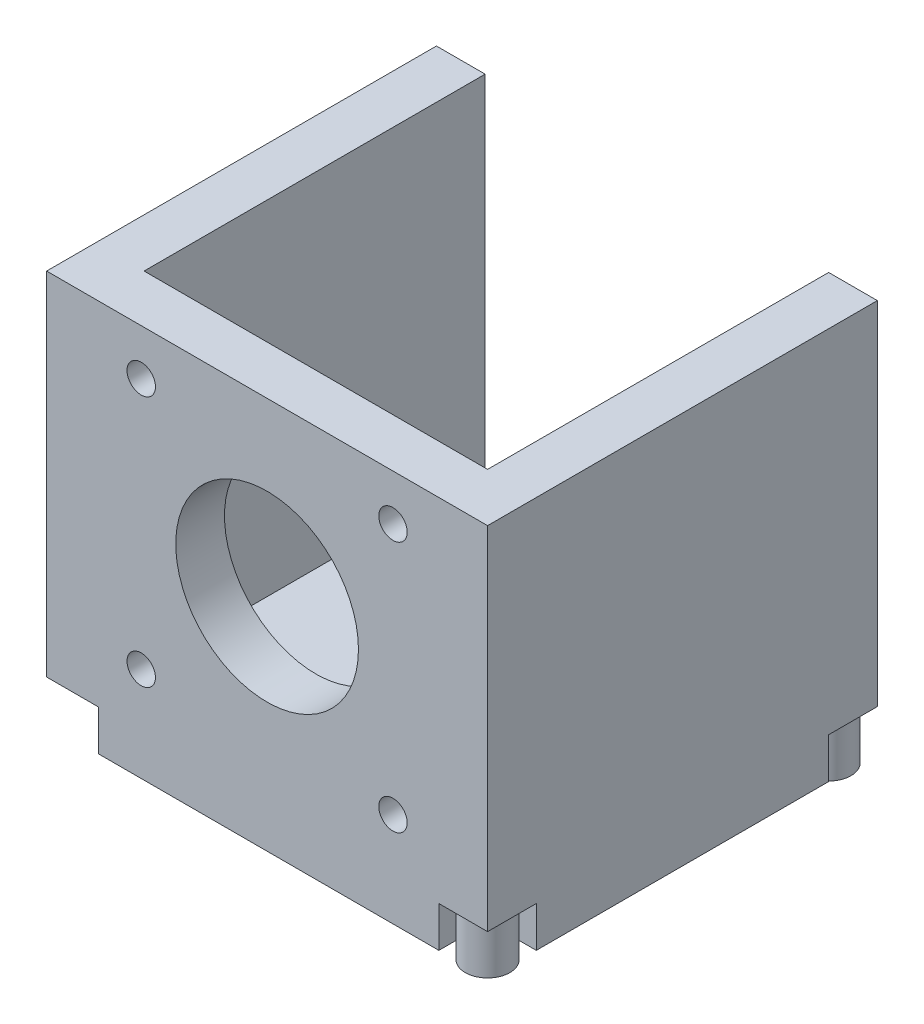
SolidWorks part; units mm, degrees
ref_plane "Спереди" through (0, 0, 0) normal (0, 0, 1) x (1, 0, 0)
ref_plane "Сверху" through (0, 0, 0) normal (0, 1, 0) x (1, 0, 0)
ref_plane "Справа" through (0, 0, 0) normal (1, 0, 0) x (0, 0, -1)
sketch "Эскиз1" plane through (0, 0, 0) normal (0, 0, 1) x (1, 0, 0)
  line L0 (21.15, 42.3) -> (21.15, 0) construction
  line L1 (42.3, 42.3) -> (0, 42.3)
  line L2 (42.3, 42.3) -> (42.3, 0)
  line L3 (42.3, 0) -> (0, 0)
  line L4 (0, 42.3) -> (0, 0)
  line L5 (0, 21.15) -> (42.3, 21.15) construction
  circle A0 centre (36.65, 36.65) radius 1.75
  circle A1 centre (5.65, 36.65) radius 1.75
  circle A2 centre (5.65, 5.65) radius 1.75
  circle A3 centre (36.65, 5.65) radius 1.75
  circle A4 centre (21.15, 21.15) radius 11.25
  dimension "D3" = 3.5
  dimension "D8" = 22.5
  dimension "D1" = 42.3
  dimension "D2" = 42.3
  dimension "D4" = 15.5
  dimension "D5" = 15.5
  dimension "D6" = 2
  dimension "D7" = 2
extrude "Бобышка-Вытянуть1" add sketch "Эскиз1" along normal blind 6
sketch "Эскиз2" plane through (0, 0, 0) normal (-1, 0, 0) x (0, 0, 1)
  line L0 (6, 42.3) -> (-42, 42.3)
  line L1 (-42, 42.3) -> (-42, 0)
  line L2 (-42, 0) -> (6, 0)
  line L3 (6, 0) -> (6, 42.3)
  dimension "D1" = 48
extrude "Бобышка-Вытянуть2" add sketch "Эскиз2" along normal blind 6
sketch "Эскиз3" plane through (42.3, 0, 0) normal (1, 0, 0) x (0, 0, -1)
  line L0 (-6, 42.3) -> (42, 42.3)
  line L1 (42, 42.3) -> (42, 0)
  line L2 (42, 0) -> (-6, 0)
  line L3 (-6, 0) -> (-6, 42.3)
  dimension "D1" = 48
extrude "Бобышка-Вытянуть3" add sketch "Эскиз3" along normal blind 6
sketch "Эскиз4" plane through (0, 0, 0) normal (0, -1, 0) x (1, 0, 0)
  line L0 (-6, -42) -> (48.3, -42)
  line L1 (48.3, -42) -> (48.3, 6)
  line L2 (48.3, 6) -> (-6, 6)
  line L3 (-6, 6) -> (-6, -42)
extrude "Бобышка-Вытянуть4" add sketch "Эскиз4" along normal blind 6
sketch "Эскиз5" plane through (0, -6, 0) normal (0, -1, 0) x (1, 0, 0)
  line L0 (-6, -42) -> (0, -42)
  line L1 (-6, -42) -> (48.3, -42) construction
  line L2 (0, -42) -> (0, -36)
  line L3 (0, -36) -> (-6, -36)
  line L4 (-6, 6) -> (-6, -42) construction
  line L5 (-6, -36) -> (-6, -42)
  line L6 (-6, -42) -> (-6.0397, -42.0334)
  line L7 (-6, 6) -> (-6, 0)
  line L8 (-6, 0) -> (0.36, 0)
  line L9 (0.36, 0) -> (0.36, 6)
  line L10 (48.3, 6) -> (-6, 6) construction
  line L11 (48.3, -42) -> (42.3, -42)
  line L12 (42.3, -42) -> (42.3, -36)
  line L13 (42.3, -36) -> (48.3, -36)
  line L14 (48.3, -42) -> (48.3, 6) construction
  line L15 (48.3, -36) -> (48.3, -42)
  line L16 (48.3, -42) -> (48.258, -42.2073)
  line L17 (48.3, 6) -> (48.3, 0)
  line L18 (48.3, 0) -> (42.3, 0)
  line L19 (42.3, 0) -> (42.3, 6)
  line L20 (42.3, 6) -> (48.3, 6)
  line L21 (48.3, 6) -> (48.2471, 6.051)
  line M1 (-6, 6) -> (-6, -42)
  line M2 (-6, -42) -> (48.3, -42)
  line M3 (48.3, -42) -> (48.3, 6)
  line M4 (48.3, 6) -> (-6, 6)
  dimension "D1" = 6
  dimension "D2" = 6
  dimension "D3" = 6
extrude "Вырез-Вытянуть1" cut sketch "Эскиз5" against normal blind 5 contours L13 L12 M2 M3 | L2 L3 M1 M2 | L8 L9 M4 M1 | L19 L18 M3 M4
sketch "Эскиз6" plane through (0, -1, 0) normal (0, -1, 0) x (1, 0, 0)
  circle A0 centre (45.3, 3) radius 2.75
  dimension "D1" = 5.5
extrude "Бобышка-Вытянуть5" add sketch "Эскиз6" along normal blind 6
sketch "Эскиз7" plane through (0, -1, 0) normal (0, -1, 0) x (1, 0, 0)
  circle A0 centre (45.3, -39) radius 2.75
  dimension "D1" = 5.5
extrude "Бобышка-Вытянуть6" add sketch "Эскиз7" along normal blind 6
